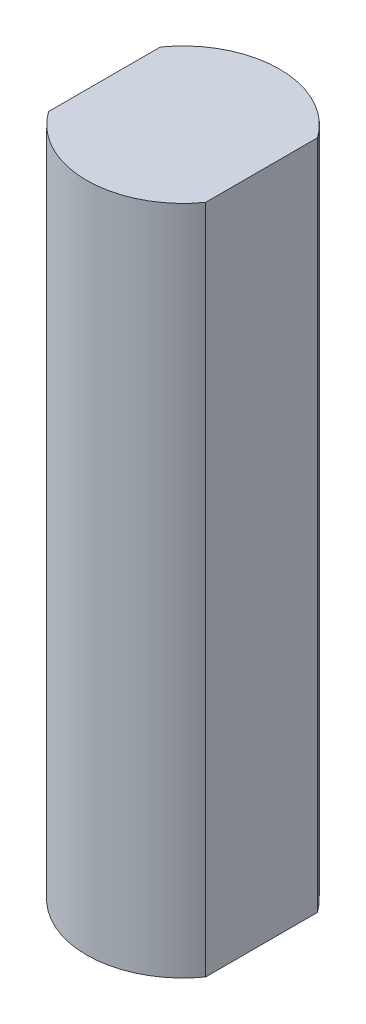
SolidWorks part; units mm, degrees
ref_plane "Front Plane" through (0, 0, 0) normal (0, 0, 1) x (1, 0, 0)
ref_plane "Top Plane" through (0, 0, 0) normal (0, 1, 0) x (1, 0, 0)
ref_plane "Right Plane" through (0, 0, 0) normal (1, 0, 0) x (0, 0, -1)
sketch "Sketch1" plane through (0, 0, 0) normal (0, 1, 0) x (1, 0, 0)
  circle A0 centre (0, 0) radius 4.3815
  dimension "D1" = 8.763
extrude "Boss-Extrude1" add sketch "Sketch1" along normal blind 30.48
sketch "Sketch2" plane through (0, 30.48, 0) normal (0, 1, 0) x (1, 0, 0)
  line L0 (3.5701, 2.54) -> (3.5701, -2.54)
  line L1 (-3.5701, 2.54) -> (-3.5701, -2.54)
  circle A0 centre (0, 0) radius 4.3815 construction
  circle M3 centre (0, 0) radius 4.3815
  dimension "D1" = 5.08
  dimension "D2" = 5.08
extrude "Cut-Extrude1" cut sketch "Sketch2" against normal blind 48.26 contours L1 M3 | L0 M3
